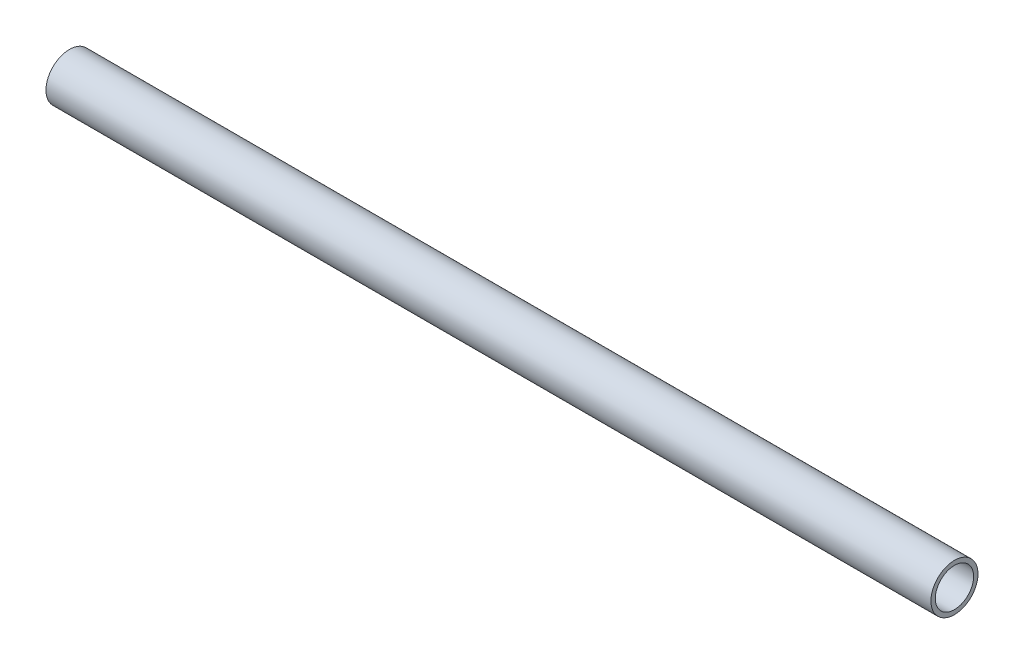
SolidWorks part; units mm, degrees
ref_plane "Front" through (0, 0, 0) normal (0, 0, 1) x (1, 0, 0)
ref_plane "Top" through (0, 0, 0) normal (0, 1, 0) x (1, 0, 0)
ref_plane "Right" through (0, 0, 0) normal (1, 0, 0) x (0, 0, -1)
sketch "Sketch1" plane through (0, 0, 0) normal (0, 0, 1) x (1, 0, 0)
  line L0 (0, 0) -> (298.45, 0)
  dimension "D1" = 298.45
other "Structural Member1"
ref_plane "Plane1" through (0, 0, 0) normal (1, 0, 0) x (0, 1, 0)
sketch "Sketch11" plane through (0, 0, 0) normal (1, 0, 0) x (0, 1, 0)
  circle A0 centre (0, 0) radius 6.4643
  circle A1 centre (0, 0) radius 7.9375
  point P5 (0, 0)
  dimension "Out_dia" = 15.875
  dimension "D1" = 1.4732
